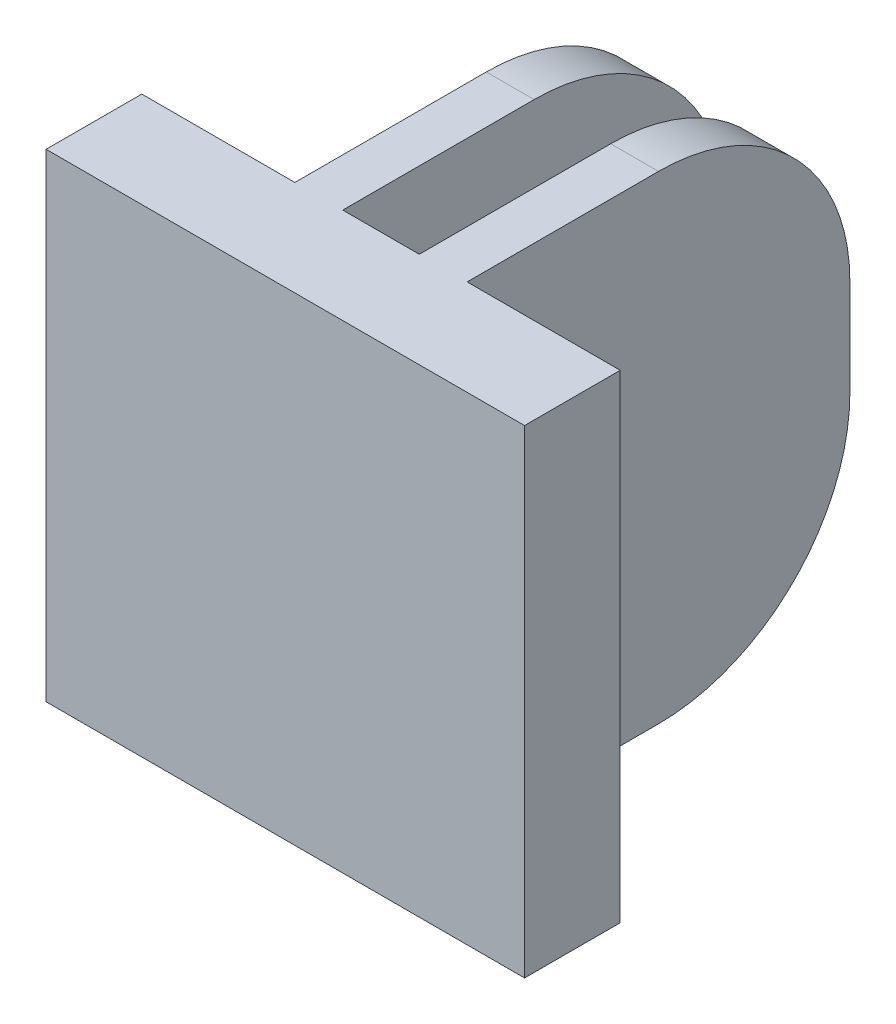
SolidWorks part; units mm, degrees
ref_plane "Płaszczyzna przednia" through (0, 0, 0) normal (0, 0, 1) x (1, 0, 0)
ref_plane "Płaszczyzna górna" through (0, 0, 0) normal (0, 1, 0) x (1, 0, 0)
ref_plane "Płaszczyzna prawa" through (0, 0, 0) normal (1, 0, 0) x (0, 0, -1)
sketch "Szkic1" plane through (0, 0, 0) normal (0, 0, 1) x (1, 0, 0)
  line L1 (-25, -25) -> (25, -25)
  line L2 (-25, -25) -> (-25, 25)
  line L3 (-25, 25) -> (25, 25)
  line L4 (25, -25) -> (25, 25)
  line L5 (-25, -25) -> (25, 25) construction
  line L6 (-25, 25) -> (25, -25) construction
  point P0 (0, 0)
  dimension "D1" = 50
  dimension "D2" = 50
extrude "Dodanie-wyciągnięcie1" add sketch "Szkic1" along normal blind 10
sketch "Szkic2" plane through (0, 0, 0) normal (0, 0, -1) x (-1, 0, 0)
  line L0 (-25, 0) -> (-9, 0) construction
  line L1 (-25, -25) -> (-25, 25) construction
  line L2 (-9, -25) -> (-9, 25)
  line L3 (-25, 25) -> (25, 25) construction
  line L4 (-9, 25) -> (-4, 25)
  line L5 (-4, 25) -> (-4, -25)
  line L6 (25, -25) -> (-25, -25) construction
  line L7 (-4, -25) -> (-9, -25)
  line L8 (0, 25) -> (0, -26.3928) construction
  line L9 (4, -25) -> (9, -25)
  line L10 (4, 25) -> (4, -25)
  line L11 (9, 25) -> (4, 25)
  line L12 (9, -25) -> (9, 25)
  point P10 (-9, 0)
  dimension "D1" = 16
extrude "Dodanie-wyciągnięcie2" add sketch "Szkic2" along normal blind 40
sketch "Szkic4" plane through (9, 0, 0) normal (1, 0, 0) x (0, 0, -1)
  line L0 (0, 25) -> (-10, 25)
  line L1 (20, 25) -> (0, 25)
  line L2 (40, 5) -> (40, -5)
  line L3 (20, -25) -> (0, -25)
  line L4 (-10, 25) -> (-10, -25)
  line L5 (-10, -25) -> (0, -25)
  arc A0 (40, -5) -> (20, -25) centre (20, -5) cw
  arc A1 (20, 25) -> (40, 5) centre (20, 5) cw
  point P10 (40, 25)
  dimension "D1" = 20
extrude "Wycięcie-wyciągnięcie-cienka ścianka2" cut sketch "Szkic4" against normal blind 40 thin
sketch "Szkic5" plane through (0, 0, 10) normal (0, 0, 1) x (1, 0, 0)
  circle A0 centre (0, 0) radius 20.6682
